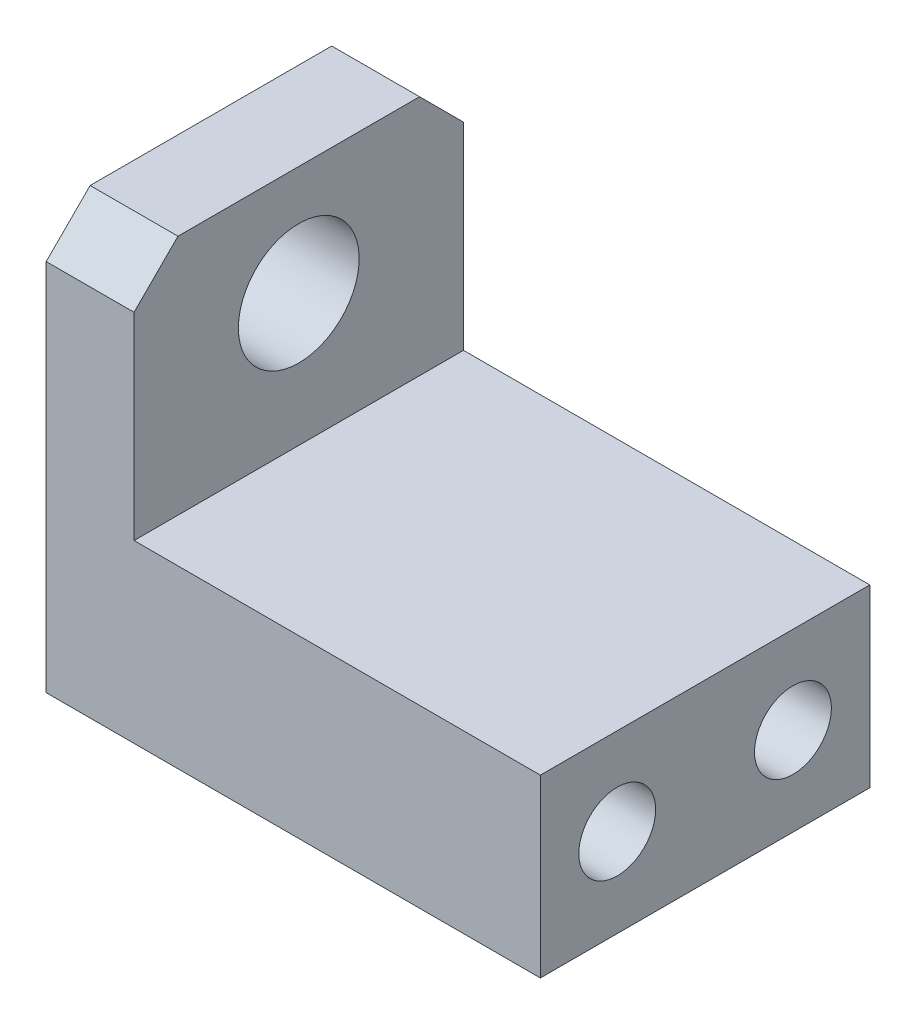
SolidWorks part; units mm, degrees
ref_plane "Front Plane" through (0, 0, 0) normal (0, 0, 1) x (1, 0, 0)
ref_plane "Top Plane" through (0, 0, 0) normal (0, 1, 0) x (1, 0, 0)
ref_plane "Right Plane" through (0, 0, 0) normal (1, 0, 0) x (0, 0, -1)
sketch "Sketch1" plane through (0, 0, 0) normal (0, 0, 1) x (1, 0, 0)
  line L0 (-2.1353, 2.0602) -> (1.8647, 2.0602)
  line L1 (1.8647, 2.0602) -> (1.8647, -8.9398)
  line L2 (1.8647, -8.9398) -> (20.3647, -8.9398)
  line L3 (20.3647, -8.9398) -> (20.3647, -16.9398)
  line L4 (20.3647, -16.9398) -> (-2.1353, -16.9398)
  line L5 (-2.1353, -16.9398) -> (-2.1353, 2.0602)
  dimension "D1" = 4
  dimension "D2" = 11
  dimension "D3" = 19
  dimension "D4" = 22.5
extrude "Boss-Extrude1" add sketch "Sketch1" along normal blind 15
sketch "Sketch2" plane through (-2.1353, 0, 0) normal (-1, 0, 0) x (0, 0, 1)
  line L0 (15, 2.0602) -> (0, 2.0602) construction
  line L1 (0, 2.0602) -> (0, -16.9398) construction
  line L2 (15, 2.0602) -> (0, 2.0602) construction
  circle A0 centre (7.5, -2.9398) radius 2.75
  circle A1 centre (3.5, -12.9147) radius 1.75
  circle A2 centre (11.5, -12.9147) radius 1.75
  circle A3 centre (11.5, -12.9147) radius 3
  circle A4 centre (3.5, -12.9147) radius 3
  point P13 (7.5, 2.0602)
  dimension "D1" = 3.5
  dimension "D2" = 6
  dimension "D4" = 8
  dimension "D5" = 5.5
  dimension "D3" = 3.5
  dimension "D6" = 5
extrude "Cut-Extrude1" cut sketch "Sketch2" against normal blind 15
sketch "Sketch3" plane through (-2.1353, 0, 0) normal (-1, 0, 0) x (0, 0, 1)
  circle A0 centre (3.5, -12.9147) radius 1.75
  circle A1 centre (11.5, -12.9147) radius 1.75
extrude "Cut-Extrude2" cut sketch "Sketch3" against normal through all
chamfer "Chamfer1" distance 2 angle 45 2 edges at (-0.1353, 2.0602, 0) (-0.1353, 2.0602, 15)
